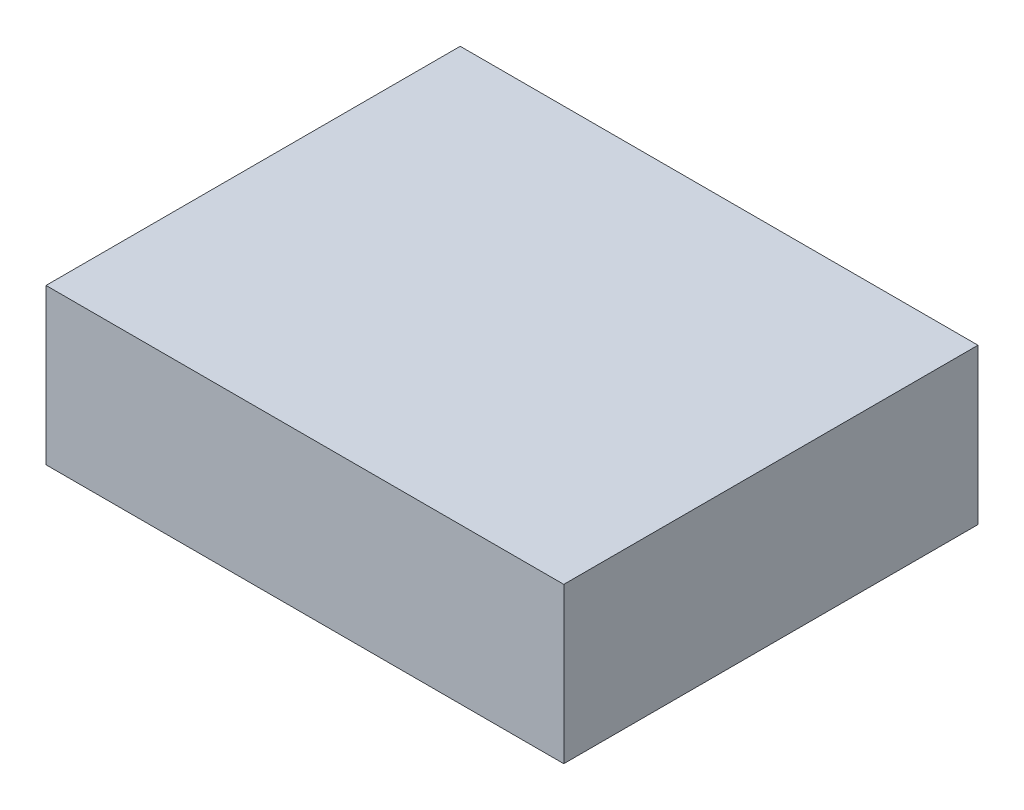
SolidWorks part; units mm, degrees
ref_plane "Front Plane" through (0, 0, 0) normal (0, 0, 1) x (1, 0, 0)
ref_plane "Top Plane" through (0, 0, 0) normal (0, 1, 0) x (1, 0, 0)
ref_plane "Right Plane" through (0, 0, 0) normal (1, 0, 0) x (0, 0, -1)
sketch "Sketch1" plane through (0, 0, 0) normal (0, 1, 0) x (1, 0, 0)
  line L1 (50, -40) -> (-50, -40)
  line L2 (50, -40) -> (50, 40)
  line L3 (50, 40) -> (-50, 40)
  line L4 (-50, -40) -> (-50, 40)
  line L5 (50, -40) -> (-50, 40) construction
  line L6 (50, 40) -> (-50, -40) construction
  point P0 (0, 0)
  dimension "D1" = 80
  dimension "D2" = 100
extrude "Boss-Extrude1" add sketch "Sketch1" along normal blind 30
